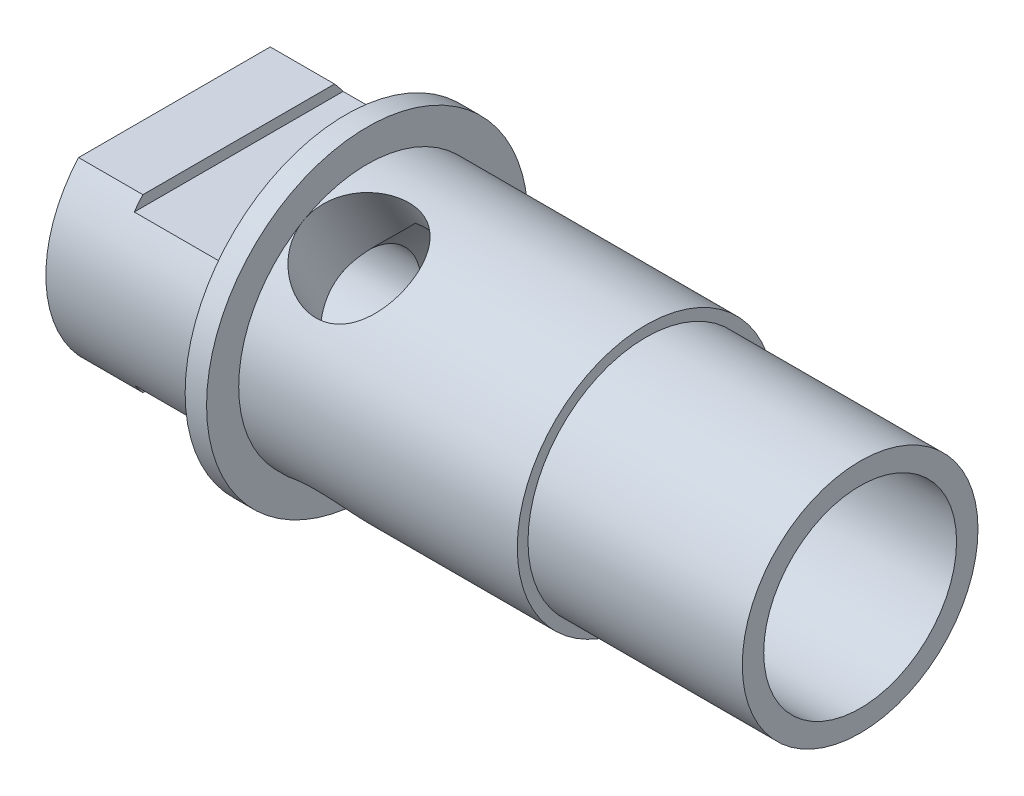
SolidWorks part; units mm, degrees
ref_plane "Plan de face" through (0, 0, 0) normal (0, 0, 1) x (1, 0, 0)
ref_plane "Plan de dessus" through (0, 0, 0) normal (0, 1, 0) x (1, 0, 0)
ref_plane "Plan de droite" through (0, 0, 0) normal (1, 0, 0) x (0, 0, -1)
sketch "Esquisse1" plane through (0, 0, 0) normal (0, 0, 1) x (1, 0, 0)
  line L0 (-18.7022, 0) -> (29.1079, 0) construction
  line L1 (-2.5, 2.5) -> (-0.5, 4.5)
  line L2 (-0.5, 4.5) -> (20.5, 4.5)
  line L3 (20.5, 4.5) -> (20.5, 5.5)
  line L4 (20.5, 5.5) -> (10.5, 5.5)
  line L5 (10.5, 5.5) -> (10.5, 6)
  line L6 (10.5, 6) -> (-2.5, 6)
  line L7 (-2.5, 6) -> (-2.5, 7.5)
  line L8 (-2.5, 7.5) -> (-3.5, 7.5)
  line L9 (-3.5, 7.5) -> (-3.5, 3.9377)
  line L11 (-3.5, 3.9377) -> (-3.5, 6)
  line L12 (-3.5, 6) -> (-11.5, 6)
  line L13 (-11.5, 6) -> (-11.5, 2.5)
  line L14 (-11.5, 2.5) -> (-2.5, 2.5)
  dimension "D1" = 10
  dimension "D3" = 8
  dimension "D4" = 1
  dimension "D5" = 20.5
  dimension "D6" = 32
  dimension "D8" = 21
  dimension "D9" = 2.5
  dimension "D10" = 6
  dimension "D11" = 4.5
  dimension "D12" = 5.5
  dimension "D13" = 6
  dimension "D14" = 7.5
revolve "Révolution1" add sketch "Esquisse1" angle 360 about L0
sketch "Esquisse2" plane through (-11.5, 0, 0) normal (-1, 0, 0) x (0, 0, 1)
  line L0 (-6, 0) -> (6, 0) construction
  line L1 (-4.4721, 4) -> (4.4721, 4)
  line L2 (-4.4721, -4) -> (4.4721, -4)
  circle A0 centre (0, 0) radius 6 construction
  circle A1 centre (0, 0) radius 6 construction
  arc A3 (-4.4721, -4) -> (4.4721, -4) centre (0, 0) ccw
  arc A4 (4.4721, 4) -> (-4.4721, 4) centre (0, 0) ccw
  dimension "D1" = 4
  dimension "D2" = 4
extrude "Enlèv. mat.-Extru.1" cut sketch "Esquisse2" against normal blind 8
sketch "Esquisse3" plane through (0, 4, 0) normal (0, 1, 0) x (1, 0, 0)
  line L1 (-3.5, 4.4721) -> (-3.5, -4.4721) construction
  line L2 (-3.5, 5) -> (-8.5, 5)
  line L3 (-3.5, 5) -> (-3.5, -5)
  line L4 (-3.5, -5) -> (-8.5, -5)
  line L5 (-8.5, 5) -> (-8.5, -5)
  line L6 (-11.5, 4.4721) -> (-11.5, -4.4721) construction
  point P7 (-11.5, 0)
  point P8 (-8.5, 0)
  dimension "D1" = 5
  dimension "D2" = 10
extrude "Enlèv. mat.-Extru.2" cut sketch "Esquisse3" against normal blind 0.5
mirror "Symétrie1" about plane through (0, 0, 0) normal (0, 1, 0) of "Enlèv. mat.-Extru.2"
sketch "Esquisse4" plane through (0, 0, 0) normal (0, 0, 1) x (1, 0, 0)
  circle A0 centre (0, 0) radius 2.5
  dimension "D1" = 5
extrude "Enlèv. mat.-Extru.3" cut sketch "Esquisse4" against normal blind 7.5
pattern_circular "Répétition circulaire1" count 3 over 360 about axis through (-18.7022, 0, 0) along (-1, 0, 0) of "Enlèv. mat.-Extru.3"
